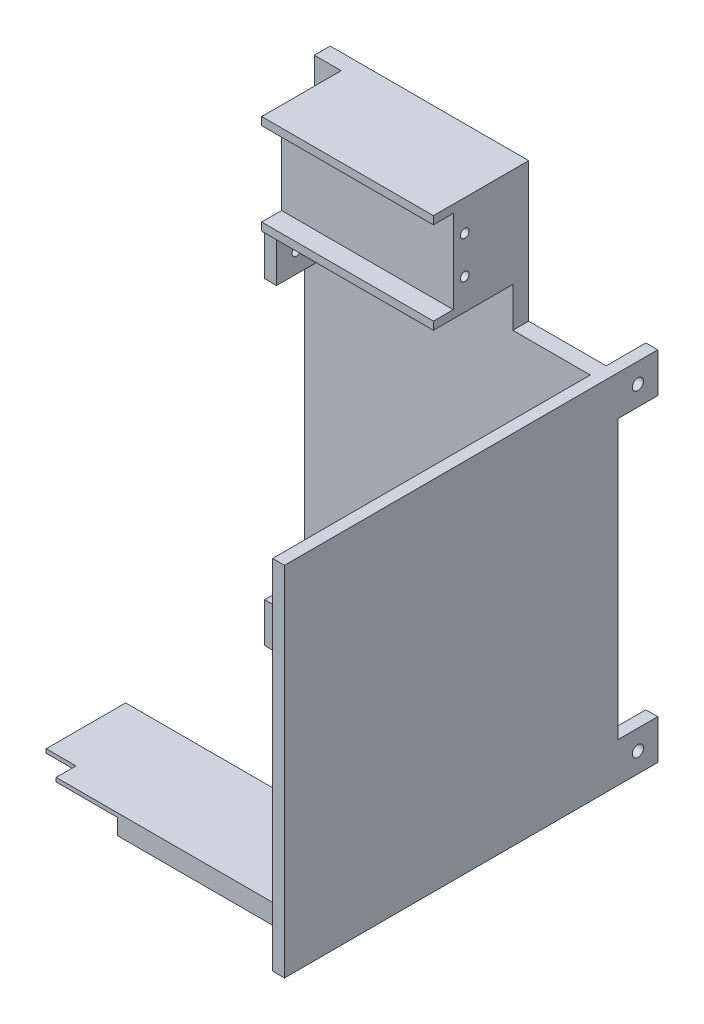
SolidWorks part; units mm, degrees
ref_plane "前基準面" through (0, 0, 0) normal (0, 0, 1) x (1, 0, 0)
ref_plane "上基準面" through (0, 0, 0) normal (0, 1, 0) x (1, 0, 0)
ref_plane "右基準面" through (0, 0, 0) normal (1, 0, 0) x (0, 0, -1)
sketch "草圖1" plane through (0, 0, 0) normal (0, 0, 1) x (1, 0, 0)
  line L0 (0, -55) -> (0, 55) construction
  line L1 (-37.5, 45) -> (-35, 45)
  line L2 (-37.5, 45) -> (-37.5, -45)
  line L3 (-37.5, -45) -> (37.5, -45)
  line L4 (37.5, 45) -> (37.5, -45)
  line L5 (55, 0) -> (-55, 0) construction
  line L6 (15, 45) -> (37.5, 45)
  line L8 (-35, 45) -> (-35, 80)
  line L9 (-35, 80) -> (15, 80)
  line L10 (15, 45) -> (15, 80)
  dimension "D1" = 75
  dimension "D2" = 90
  dimension "D3" = 37.5
  dimension "D4" = 45
  dimension "D5" = 35
  dimension "D6" = 35
  dimension "D7" = 50
extrude "填料-伸長1" add sketch "草圖1" along normal blind 4 contours L1 L10 L9 L8 | L4 L1 L2 L3
sketch "草圖3" plane through (0, 0, 4) normal (0, 0, 1) x (1, 0, 0)
  line L0 (-35, 80) -> (15, 80) construction
  line L1 (-28.2355, 57) -> (15, 57)
  line L2 (-28.2355, 57) -> (-28.2355, 55)
  line L3 (-28.2355, 55) -> (15, 55)
  line L4 (15, 57) -> (15, 55)
  line L5 (-28.2355, 80) -> (15, 80)
  line L6 (-28.2355, 80) -> (-28.2355, 78)
  line L7 (-28.2355, 78) -> (15, 78)
  line L8 (15, 80) -> (15, 78)
  dimension "D1" = 2
  dimension "D2" = 2
  dimension "D3" = 21
extrude "填料-伸長2" add sketch "草圖3" along normal blind 20
sketch "草圖4" plane through (0, 0, 4) normal (0, 0, 1) x (1, 0, 0)
  line L1 (-28.2355, 78) -> (15, 78)
  line L2 (-28.2355, 78) -> (-28.2355, 57)
  line L3 (-28.2355, 57) -> (15, 57)
  line L4 (15, 78) -> (15, 57)
extrude "填料-伸長3" add sketch "草圖4" along normal blind 15
sketch "草圖8" plane through (0, 0, 0) normal (0, 0, -1) x (-1, 0, 0)
  line L1 (-37.5, 45) -> (-34.5, 45)
  line L2 (-37.5, 45) -> (-37.5, 35)
  line L3 (-37.5, 35) -> (-34.5, 35)
  line L4 (-34.5, 45) -> (-34.5, 35)
  line L5 (37.5, 45) -> (34.5, 45)
  line L6 (37.5, 45) -> (37.5, 35)
  line L7 (37.5, 35) -> (34.5, 35)
  line L8 (34.5, 45) -> (34.5, 35)
  line L9 (37.5, -45) -> (34.5, -45)
  line L10 (37.5, -45) -> (37.5, -35)
  line L11 (37.5, -35) -> (34.5, -35)
  line L12 (34.5, -45) -> (34.5, -35)
  line L13 (-37.5, -45) -> (-34.5, -45)
  line L14 (-37.5, -45) -> (-37.5, -35)
  line L15 (-37.5, -35) -> (-34.5, -35)
  line L16 (-34.5, -45) -> (-34.5, -35)
  dimension "D1" = 3
  dimension "D2" = 3
  dimension "D3" = 10
  dimension "D4" = 10
  dimension "D5" = 10
  dimension "D6" = 3
  dimension "D7" = 10
  dimension "D8" = 3
extrude "填料-伸長4" add sketch "草圖8" along normal blind 10
sketch "草圖10" plane through (37.5, 0, 0) normal (1, 0, 0) x (0, 0, -1)
  line L0 (10, 45) -> (10, 35) construction
  line L1 (-4, 45) -> (10, 45) construction
  line L2 (10, -35) -> (0, -35) construction
  line L3 (10, -35) -> (10, -45) construction
  circle A0 centre (5, 40) radius 1.4
  circle A1 centre (5, -40) radius 1.4
  dimension "D1" = 2.8
  dimension "D4" = 2.8
  dimension "D2" = 5
  dimension "D3" = 5
  dimension "D5" = 5
  dimension "D6" = 5
extrude "除料-伸長1" cut sketch "草圖10" against normal blind 83
sketch "草圖11" plane through (0, 0, 4) normal (0, 0, 1) x (1, 0, 0)
  line L5 (37.5, 45) -> (34.5, 45)
  line L6 (37.5, 45) -> (37.5, -45)
  line L7 (37.5, -45) -> (34.5, -45)
  line L8 (34.5, 45) -> (34.5, -45)
extrude "填料-伸長5" add sketch "草圖11" along normal blind 80
sketch "草圖12" plane through (0, -45, 0) normal (0, -1, 0) x (1, 0, 0)
  line L0 (37.5, 84) -> (37.5, -10) construction
  line L2 (-37.5, 74) -> (-37.5, 49)
  line L3 (-37.5, 49) -> (37.5, 49)
  line L4 (37.5, 74) -> (37.5, 49)
  line L6 (-37.5, 74) -> (37.5, 74)
  dimension "D1" = 25
  dimension "D2" = 75
  dimension "D3" = 0
extrude "填料-伸長6" add sketch "草圖12" against normal blind 5
sketch "草圖13" plane through (0, -45, 0) normal (0, -1, 0) x (1, 0, 0)
  line L0 (34.5, 74) -> (-37.5, 74) construction
  line L1 (-37.5, 74) -> (-14.5, 74)
  line L2 (-37.5, 74) -> (-37.5, 54)
  line L3 (-37.5, 54) -> (-14.5, 54)
  line L4 (-14.5, 74) -> (-14.5, 54)
  line L6 (-37.5, 74) -> (-37.5, 49) construction
  dimension "D1" = 20
  dimension "D2" = 23
  dimension "D3" = 0
extrude "除料-伸長2" cut sketch "草圖13" against normal blind 4
sketch "草圖14" plane through (0, -41, 0) normal (0, -1, 0) x (1, 0, 0)
  line L0 (-14.5, 74) -> (-37.5, 74) construction
  line L1 (-37.5, 74) -> (-30, 74)
  line L2 (-37.5, 74) -> (-37.5, 69)
  line L3 (-37.5, 69) -> (-30, 69)
  line L4 (-30, 74) -> (-30, 69)
  line L7 (-37.5, 74) -> (-37.5, 54) construction
  dimension "D1" = 5
  dimension "D2" = 7.5
  dimension "D3" = 0
extrude "除料-伸長3" cut sketch "草圖14" against normal up to next
sketch "草圖15" plane through (15, 0, 0) normal (1, 0, 0) x (0, 0, -1)
  line L0 (-24, 78) -> (-19, 78) construction
  line L1 (-19, 57) -> (-19, 78) construction
  line L3 (-24, 57) -> (-19, 57) construction
  circle A0 centre (-16.1, 72.2) radius 1.1
  circle A1 centre (-16.1, 62.8) radius 1.1
  dimension "D1" = 5.8
  dimension "D2" = 2.9
  dimension "D3" = 2.9
  dimension "D4" = 5.8
extrude "除料-伸長4" cut sketch "草圖15" against normal blind 10
sketch "草圖17" plane through (0, 0, 4) normal (0, 0, 1) x (1, 0, 0)
  line L1 (-37.5, 45) -> (-34.5, 45)
  line L2 (-37.5, 45) -> (-37.5, 35)
  line L3 (-37.5, 35) -> (-34.5, 35)
  line L4 (-34.5, 45) -> (-34.5, 35)
  dimension "D1" = 3
  dimension "D2" = 10
extrude "填料-伸長7" add sketch "草圖17" along normal blind 10
sketch "草圖18" plane through (-37.5, 0, 0) normal (-1, 0, 0) x (0, 0, 1)
  line L0 (14, 45) -> (14, 35) construction
  line L1 (14, 45) -> (-10, 45) construction
  circle A0 centre (9, 40) radius 1.1
  dimension "D1" = 5
  dimension "D2" = 5
extrude "除料-伸長5" cut sketch "草圖18" against normal blind 3 contours A0
sketch "草圖19" plane through (0, 0, 4) normal (0, 0, 1) x (1, 0, 0)
  line L0 (-37.5, 35) -> (-37.5, -45) construction
  line L1 (-37.5, -35) -> (-34.5, -35)
  line L2 (-37.5, -35) -> (-37.5, -45)
  line L3 (-37.5, -45) -> (-34.5, -45)
  line L4 (-34.5, -35) -> (-34.5, -45)
  line L5 (-37.5, -45) -> (34.5, -45) construction
  dimension "D1" = 10
  dimension "D2" = 3
extrude "填料-伸長8" add sketch "草圖19" along normal blind 10
sketch "草圖20" plane through (-37.5, 0, 0) normal (-1, 0, 0) x (0, 0, 1)
  line L0 (14, -35) -> (4, -35) construction
  line L1 (14, -35) -> (14, -45) construction
  circle A0 centre (9, -40) radius 1.1
  dimension "D1" = 5
  dimension "D2" = 5
extrude "除料-伸長6" cut sketch "草圖20" against normal blind 3
